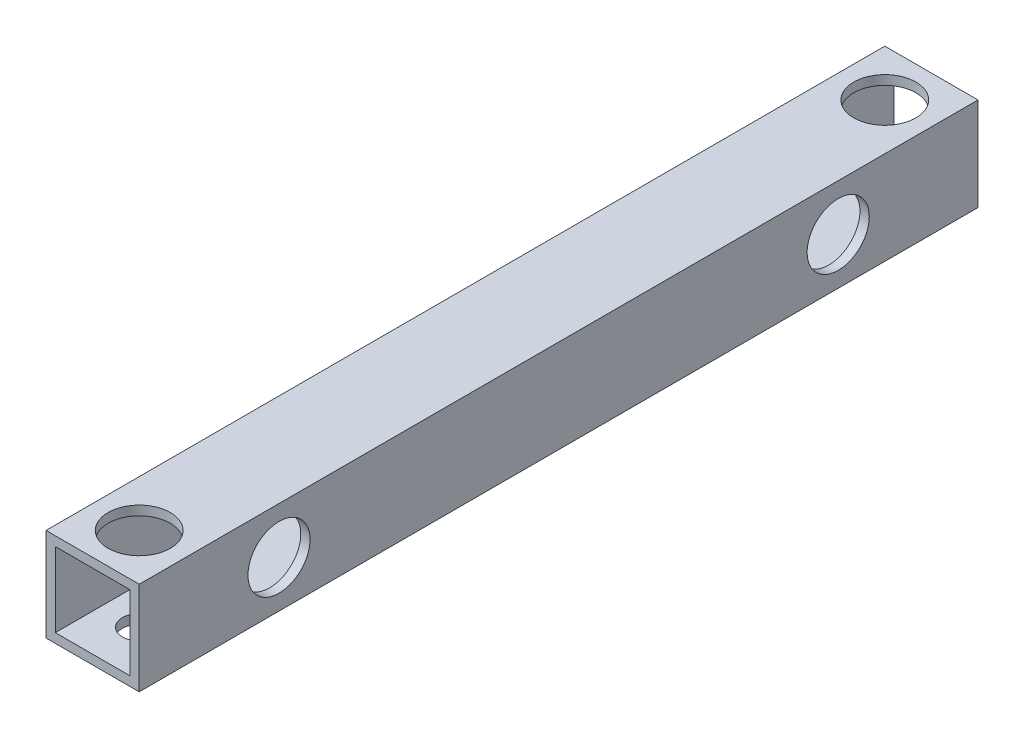
SolidWorks part; units mm, degrees
material "6063-T5"
ref_plane "正面" through (0, 0, 0) normal (0, 0, 1) x (1, 0, 0)
ref_plane "平面" through (0, 0, 0) normal (0, 1, 0) x (1, 0, 0)
ref_plane "右側面" through (0, 0, 0) normal (1, 0, 0) x (0, 0, -1)
sketch "ｽｹｯﾁ1" plane through (0, 0, 0) normal (0, 0, 1) x (1, 0, 0)
  line L1 (-7.5, -7.5) -> (7.5, -7.5)
  line L2 (-7.5, -7.5) -> (-7.5, 7.5)
  line L3 (-7.5, 7.5) -> (7.5, 7.5)
  line L4 (7.5, -7.5) -> (7.5, 7.5)
  line L5 (-7.5, -7.5) -> (7.5, 7.5) construction
  line L6 (-7.5, 7.5) -> (7.5, -7.5) construction
  line L7 (-6, -6) -> (6, -6)
  line L8 (-6, -6) -> (-6, 6)
  line L9 (-6, 6) -> (6, 6)
  line L10 (6, -6) -> (6, 6)
  line L11 (-6, -6) -> (6, 6) construction
  line L12 (-6, 6) -> (6, -6) construction
  point P0 (0, 0)
  point P6 (0, 0)
  dimension "D1" = 1.5
  dimension "D2" = 15
  dimension "D3" = 15
extrude "ﾎﾞｽ - 押し出し1" add sketch "ｽｹｯﾁ1" along normal blind 135
sketch "ｽｹｯﾁ2" plane through (7.5, 0, 0) normal (1, 0, 0) x (0, 0, -1)
  line L0 (-135, -7.5) -> (0, -7.5) construction
  line L2 (-135, -7.5) -> (-135, 7.5) construction
  circle A4 centre (-112.5, 0) radius 2.7
  circle A8 centre (-22.5, 0) radius 2.7
  dimension "D1" = 5.4
  dimension "D2" = 22.5
  dimension "D3" = 7.5
  dimension "D4" = 90
  dimension "D9" = 2
extrude "ｶｯﾄ - 押し出し1" cut sketch "ｽｹｯﾁ2" against normal blind 25
sketch "ｽｹｯﾁ3" plane through (0, 7.5, 0) normal (0, 1, 0) x (1, 0, 0)
  line L2 (7.5, -135) -> (7.5, 0) construction
  circle A1 centre (0, -7.5) radius 2.7
  circle A6 centre (0, -127.5) radius 2.7
  dimension "D2" = 120
  dimension "D3" = 5.4
  dimension "D9" = 7.5
  dimension "D11" = 7.5
  dimension "D4" = 7.5
  dimension "D5" = 5.4
extrude "ｶｯﾄ - 押し出し2" cut sketch "ｽｹｯﾁ3" against normal blind 25
sketch "ｽｹｯﾁ4" plane through (0, 7.5, 0) normal (0, 1, 0) x (1, 0, 0)
  circle A0 centre (0, -127.5) radius 5
  circle A1 centre (0, -7.5) radius 5
  dimension "D1" = 10
  dimension "D2" = 10
extrude "ｶｯﾄ - 押し出し3" cut sketch "ｽｹｯﾁ4" against normal blind 10
sketch "ｽｹｯﾁ5" plane through (7.5, 0, 0) normal (1, 0, 0) x (0, 0, -1)
  circle A0 centre (-22.5, 0) radius 5
  circle A1 centre (-112.5, 0) radius 5
  dimension "D1" = 10
  dimension "D2" = 10
extrude "ｶｯﾄ - 押し出し4" cut sketch "ｽｹｯﾁ5" against normal blind 10
